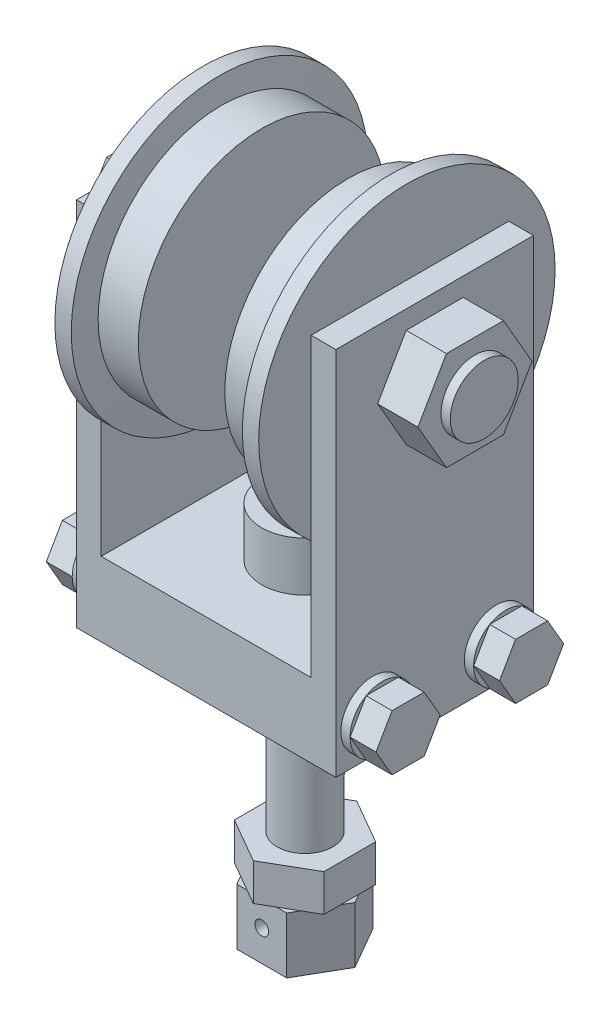
SolidWorks part; units mm, degrees
ref_plane "Front" through (0, 0, 0) normal (0, 0, 1) x (1, 0, 0)
ref_plane "Top" through (0, 0, 0) normal (0, 1, 0) x (1, 0, 0)
ref_plane "Right" through (0, 0, 0) normal (1, 0, 0) x (0, 0, -1)
ref_plane "Z PLANE" through (0, 0, 0) normal (0, 0, 1) x (1, 0, 0)
ref_plane "YOKE BOTTOM" through (0, 0, 0) normal (0, 1, 0) x (-1, 0, 0)
ref_plane "X PLANE" through (0, 0, 0) normal (1, 0, 0) x (0, 0, -1)
sketch "YOKE CROSS SECTION" plane through (0, 0, 0) normal (1, 0, 0) x (0, 0, -1)
  line L0 (0, 0) -> (0, 57.0916) construction
  line L1 (0, 84.8167) -> (0, -84.8167) construction
  line L2 (-50.8, 0) -> (50.8, 0)
  line L3 (69.1602, 0) -> (-69.1602, 0) construction
  line L4 (50.8, 0) -> (50.8, 38.1)
  line L5 (-50.8, 0) -> (-50.8, 38.1)
  line L6 (50.8, 38.1) -> (-50.8, 38.1)
  point P12 (0, 38.1)
  dimension "D1" = 38.1
  dimension "D2" = 101.6
ref_plane "1/2 YOKE LENGTH (A)" through (53.975, 0, 0) normal (1, 0, 0) x (0, 0, -1)
extrude "YOKE" add sketch "YOKE CROSS SECTION" along normal up to surface (53.975 mm away) up to plane "1/2 YOKE LENGTH (A)"
sketch "SIDEPLATE PROFILE" plane through (53.975, 0, 0) normal (1, 0, 0) x (0, 0, -1)
  line L0 (0, 0) -> (0, 74.7424) construction
  line L1 (0, 84.8167) -> (0, -84.8167) construction
  line L2 (-50.8, 0) -> (50.8, 0)
  line L3 (50.8, 0) -> (50.8, 190.5)
  line L4 (-50.8, 0) -> (-50.8, 190.5)
  line L5 (50.8, 190.5) -> (-50.8, 190.5)
  point P11 (0, 190.5)
  dimension "D1" = 190.5
ref_plane "WHEEL HEIGHT" through (0, 155.575, 0) normal (0, 1, 0) x (-1, 0, 0)
ref_plane "SCREW LOCATION X" through (0, 0, 31.75) normal (0, 0, 1) x (1, 0, 0)
ref_plane "SCREW LOCATION Y" through (0, 19.05, 0) normal (0, 1, 0) x (-1, 0, 0)
extrude "SIDEPLATE" add sketch "SIDEPLATE PROFILE" along normal blind 12.7
sketch "WHEEL PIN NUT PROFILE" plane through (66.675, 0, 0) normal (1, 0, 0) x (0, 0, -1)
  line L0 (0, 84.8167) -> (0, -84.8167) construction
  line L1 (29.3294, 155.575) -> (14.6647, 180.975)
  line L2 (14.6647, 180.975) -> (-14.6647, 180.975)
  line L3 (-14.6647, 180.975) -> (-29.3294, 155.575)
  line L4 (-29.3294, 155.575) -> (-14.6647, 130.175)
  line L5 (-14.6647, 130.175) -> (14.6647, 130.175)
  line L6 (14.6647, 130.175) -> (29.3294, 155.575)
  line L7 (69.1602, 155.575) -> (-69.1602, 155.575) construction
  circle A0 centre (0, 155.575) radius 25.4 construction
  dimension "D1" = 50.8
extrude "WHEEL PIN NUT" add sketch "WHEEL PIN NUT PROFILE" along normal blind 20.701
sketch "WHEEL PIN PROJECTION PROFILE" plane through (87.376, 0, 0) normal (1, 0, 0) x (0, 0, -1)
  line L0 (0, 84.8167) -> (0, -84.8167) construction
  line L1 (69.1602, 155.575) -> (-69.1602, 155.575) construction
  circle A0 centre (0, 155.575) radius 17.4625
  dimension "D1" = 34.925
extrude "WHEEL PIN PROJECTION" add sketch "WHEEL PIN PROJECTION PROFILE" along normal blind 4.7625
sketch "LOCKNUTS PROFILE" plane through (66.675, 0, 0) normal (1, 0, 0) x (0, 0, -1)
  line L0 (-31.75, 84.8167) -> (-31.75, -84.8167) construction
  line L1 (50, 19.05) -> (-50, 19.05) construction
  circle A0 centre (-31.75, 19.05) radius 16.4973
  dimension "D1" = 32.9946
extrude "LOCKNUTS" add sketch "LOCKNUTS PROFILE" along normal blind 4.7625
sketch "SCREWS PROFILE" plane through (71.4375, 0, 0) normal (1, 0, 0) x (0, 0, -1)
  line L0 (50, 19.05) -> (-50, 19.05) construction
  line L1 (-15.2522, 19.05) -> (-23.5011, 33.3375)
  line L2 (-23.5011, 33.3375) -> (-39.9989, 33.3375)
  line L3 (-39.9989, 33.3375) -> (-48.2478, 19.05)
  line L4 (-48.2478, 19.05) -> (-39.9989, 4.7625)
  line L5 (-39.9989, 4.7625) -> (-23.5011, 4.7625)
  line L6 (-23.5011, 4.7625) -> (-15.2522, 19.05)
  line L7 (-31.75, 84.8167) -> (-31.75, -84.8167) construction
  circle A0 centre (-31.75, 19.05) radius 14.2875 construction
  dimension "D1" = 28.575
extrude "SCREWS" add sketch "SCREWS PROFILE" along normal blind 13.3096
sketch "PROFILE" plane through (0, 38.1, 0) normal (0, 1, 0) x (-1, 0, 0)
  line L0 (84.8167, 0) -> (-84.8167, 0) construction
  line L1 (0, 83.2389) -> (0, -83.2389) construction
  circle A0 centre (0, 0) radius 22.225
  dimension "D1" = 44.45
extrude "KING BOLT HEAD" add sketch "PROFILE" along normal blind 25.4
mirror "Mirror1" about plane through (0, 0, 0) normal (0, 0, 1) of "SCREWS", "LOCKNUTS"
mirror "Mirror5" about plane through (0, 0, 0) normal (1, 0, 0) of bodies 112
ref_plane "TOP OF NUT" through (0, -82.55, 0) normal (0, 1, 0) x (-1, 0, 0)
sketch "DIA." plane through (0, 0, 0) normal (0, -1, 0) x (1, 0, 0)
  line L0 (84.8167, 0) -> (-84.8167, 0) construction
  line L1 (0, -83.2389) -> (0, 83.2389) construction
  circle A0 centre (0, 0) radius 14.2875
  dimension "D1" = 28.575
extrude "KING BOLT" add sketch "DIA." along normal up to surface (82.55 mm away) up to plane "TOP OF NUT"
sketch "KING BOLT JAN NUT PROFILE" plane through (0, -82.55, 0) normal (0, -1, 0) x (1, 0, 0)
  line L0 (84.8167, 0) -> (-84.8167, 0) construction
  line L1 (0, -26.5798) -> (23.0188, -13.2899)
  line L2 (23.0188, -13.2899) -> (23.0187, 13.2899)
  line L3 (23.0187, 13.2899) -> (0, 26.5798)
  line L4 (0, 26.5798) -> (-23.0188, 13.2899)
  line L5 (-23.0188, 13.2899) -> (-23.0188, -13.2899)
  line L6 (-23.0188, -13.2899) -> (0, -26.5798)
  line L7 (0, -83.2389) -> (0, 83.2389) construction
  circle A0 centre (0, 0) radius 23.0188 construction
  dimension "D1" = 46.0375
extrude "KING BOLT JAM NUT" add sketch "KING BOLT JAN NUT PROFILE" along normal blind 19.05
sketch "KING BOLT NUT PROFILE" plane through (0, -101.6, 0) normal (0, -1, 0) x (1, 0, 0)
  line L1 (25.6632, 0) -> (12.8316, 22.225)
  line L2 (12.8316, 22.225) -> (-12.8316, 22.225)
  line L3 (-12.8316, 22.225) -> (-25.6632, 0)
  line L4 (-25.6632, 0) -> (-12.8316, -22.225)
  line L5 (-12.8316, -22.225) -> (12.8316, -22.225)
  line L6 (12.8316, -22.225) -> (25.6632, 0)
  line L10 (0, -83.2389) -> (0, 83.2389) construction
  line L11 (84.8167, 0) -> (-84.8167, 0) construction
  circle A0 centre (0, 0) radius 22.225 construction
  dimension "D1" = 44.45
extrude "KING BOLT NUT" add sketch "KING BOLT NUT PROFILE" along normal blind 28.9306
sketch "Sketch5" plane through (0, -130.5306, 0) normal (0, -1, 0) x (1, 0, 0)
  circle A0 centre (0, 0) radius 14.2875 construction
  circle A1 centre (0, 0) radius 14.2875
extrude "EXTENDED KING BOLT" add sketch "Sketch5" along normal blind 6.35
chamfer "Chamfer1" distance 2.3812 angle 45 1 edges at (0, -136.8806, -14.2875)
ref_plane "MOUNTING REF PLANE" through (0, -34.925, 0) normal (0, 1, 0) x (-1, 0, 0)
sketch "Sketch6" plane through (0, 0, 0) normal (0, 0, 1) x (1, 0, 0)
  line L0 (52.3875, 180.975) -> (52.3875, 231.775)
  line L1 (22.225, 219.075) -> (22.225, 155.575)
  line L2 (22.225, 155.575) -> (53.975, 155.575)
  line L3 (53.975, 180.975) -> (53.975, 155.575)
  line L4 (52.3875, 180.975) -> (53.975, 180.975)
  line L5 (22.225, 219.075) -> (42.8625, 219.075)
  line L6 (42.8625, 219.075) -> (43.9736, 231.775)
  line L7 (52.3875, 231.775) -> (43.9736, 231.775)
  line L8 (69.1602, 155.575) -> (-69.1602, 155.575) construction
  line L11 (53.975, -75.0522) -> (53.975, 75.0522) construction
  dimension "D4" = 31.75
  dimension "D1" = 63.5
  dimension "D2" = 76.2
  dimension "D3" = 1.5875
  dimension "D5" = 10.0014
  dimension "D6" = 20.6375
revolve "WHEEL" add sketch "Sketch6" angle 360 about axis through (92.1385, 155.575, 0) along (-1, 0, 0)
mirror "Mirror6" about plane through (0, 0, 0) normal (1, 0, 0) of "WHEEL"
sketch "Sketch7" plane through (0, 0, 22.225) normal (0, 0, 1) x (1, 0, 0)
  line L0 (0, -83.2389) -> (0, 83.2389) construction
  line L1 (-12.8316, -130.5306) -> (-25.6632, -130.5306) construction
  circle A0 centre (0, -114.6556) radius 3.5719
  dimension "D1" = 7.1437
  dimension "D2" = 15.875
extrude "COTTER PIN HOLE" cut sketch "Sketch7" against normal up to next
sketch "Sketch8" plane through (0, 0, 0) normal (0, -1, 0) x (1, 0, 0)
  circle A0 centre (0, 0) radius 25.4
  circle A1 centre (0, 0) radius 30.1625
  dimension "D1" = 50.8
  dimension "D2" = 60.325
extrude "SPACER" add sketch "Sketch8" along normal blind 12.7
ref_plane "TREAD OF TRACK" through (0, 92.075, 0) normal (0, 1, 0) x (-1, 0, 0)
